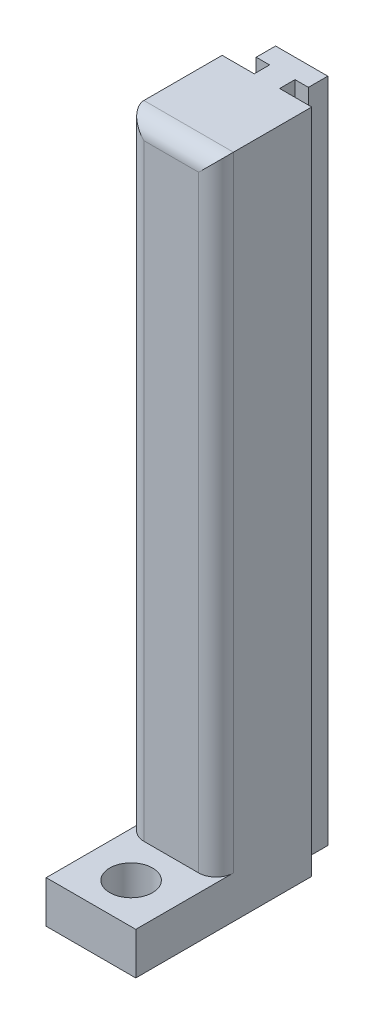
SolidWorks part; units mm, degrees
ref_plane "Front Plane" through (0, 0, 0) normal (0, 0, 1) x (1, 0, 0)
ref_plane "Top Plane" through (0, 0, 0) normal (0, 1, 0) x (1, 0, 0)
ref_plane "Right Plane" through (0, 0, 0) normal (1, 0, 0) x (0, 0, -1)
sketch "Sketch1" plane through (0, 0, 0) normal (0, 1, 0) x (1, 0, 0)
  line L1 (-4.25, 10) -> (-4.25, -10)
  line L2 (-4.25, -10) -> (4.25, -10)
  line L3 (4.25, -10) -> (4.25, 10)
  line L4 (4.25, 10) -> (-4.25, 10)
  point P0 (-4.25, 0)
  point P2 (0, 10)
  dimension "D1" = 20
  dimension "D2" = 8.5
extrude "Boss-Extrude1" add sketch "Sketch1" along normal blind 63.246
sketch "Sketch2" plane through (0, 63.246, 0) normal (0, 1, 0) x (1, 0, 0)
  line L0 (4.25, -10) -> (4.25, -2.38)
  line L1 (4.25, -10) -> (4.25, 10) construction
  line L2 (4.25, -2.38) -> (-4.25, -2.38)
  line L3 (-4.25, 10) -> (-4.25, -10) construction
  line L4 (-4.25, -2.38) -> (-4.25, -10)
  line L5 (-4.25, -10) -> (4.25, -10)
  dimension "D1" = 7.62
extrude "Cut-Extrude1" cut sketch "Sketch2" against normal offset from surface (59.246 mm away) 4 contours L2 L4 L5 L0 up to face at (0, 0, 0)
sketch "Sketch3" plane through (0, 63.246, 0) normal (0, 1, 0) x (1, 0, 0)
  line L0 (-2.4765, 10) -> (-2.4765, 8.1585)
  line L2 (4.25, 10) -> (-4.25, 10) construction
  line L3 (-2.4765, 10) -> (2.4765, 10)
  line L4 (2.4765, 10) -> (2.4765, 8.1585)
  line L5 (-2.4765, 8.1585) -> (-1.2065, 8.1585)
  line L6 (-1.2065, 8.1585) -> (-1.2065, 6.698)
  line L7 (-1.2065, 6.698) -> (1.2065, 6.698)
  line L8 (1.2065, 6.698) -> (1.2065, 8.1585)
  line L9 (1.2065, 8.1585) -> (2.4765, 8.1585)
  point P0 (0, 10)
  point P7 (0, 10)
  dimension "D1" = 4.953
  dimension "D2" = 1.8415
  dimension "D3" = 1.4605
  dimension "D4" = 1.27
  dimension "D5" = 1.4605
  dimension "D6" = 1.27
sketch "Sketch4" plane through (0, 63.246, 0) normal (0, 1, 0) x (1, 0, 0)
  line L0 (-1.2065, 6.698) -> (-4.25, 6.698)
  line L1 (-4.25, 10) -> (-4.25, -2.38) construction
  line L2 (-4.25, 6.698) -> (-4.25, 10)
  line L3 (-4.25, 10) -> (-2.4765, 10)
  line L4 (-2.4765, 10) -> (-2.4765, 8.1585)
  line L5 (-2.4765, 8.1585) -> (-1.2065, 8.1585)
  line L6 (-1.2065, 8.1585) -> (-1.2065, 6.698)
  line L7 (1.2065, 6.698) -> (4.25, 6.698)
  line L8 (4.25, -2.38) -> (4.25, 10) construction
  line L9 (4.25, 6.698) -> (4.25, 10)
  line L10 (4.25, 10) -> (2.4765, 10)
  line L11 (2.4765, 10) -> (2.4765, 8.1585)
  line L12 (2.4765, 8.1585) -> (1.2065, 8.1585)
  line L13 (1.2065, 8.1585) -> (1.2065, 6.698)
extrude "Cut-Extrude2" cut sketch "Sketch4" against normal blind 79.922 and the other way blind 5.334
sketch "Sketch5" plane through (0, 4, 0) normal (0, 1, 0) x (1, 0, 0)
  circle A0 centre (0, -6.19) radius 2.032
  dimension "D1" = 4.064
extrude "Cut-Extrude3" cut sketch "Sketch5" against normal blind 79.922
fillet "Fillet1" radius 1.651 3 edges at (4.25, 33.623, 2.38) (-4.25, 33.623, 2.38) (0, 63.246, 2.38)
